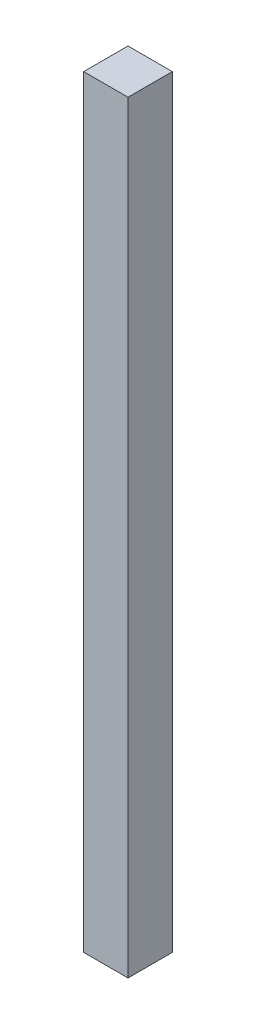
SolidWorks part; units mm, degrees
ref_plane "Front Plane" through (0, 0, 0) normal (0, 0, 1) x (1, 0, 0)
ref_plane "Top Plane" through (0, 0, 0) normal (0, 1, 0) x (1, 0, 0)
ref_plane "Right Plane" through (0, 0, 0) normal (1, 0, 0) x (0, 0, -1)
sketch "Sketch1" plane through (0, 0, 0) normal (0, 1, 0) x (1, 0, 0)
  line L1 (7.5, 7.5) -> (-7.5, 7.5)
  line L2 (7.5, 7.5) -> (7.5, -7.5)
  line L3 (7.5, -7.5) -> (-7.5, -7.5)
  line L4 (-7.5, 7.5) -> (-7.5, -7.5)
  line L5 (7.5, 7.5) -> (-7.5, -7.5) construction
  line L6 (7.5, -7.5) -> (-7.5, 7.5) construction
  point P0 (0, 0)
  dimension "D1" = 15
  dimension "D2" = 15
extrude "Boss-Extrude1" add sketch "Sketch1" along normal blind 258
